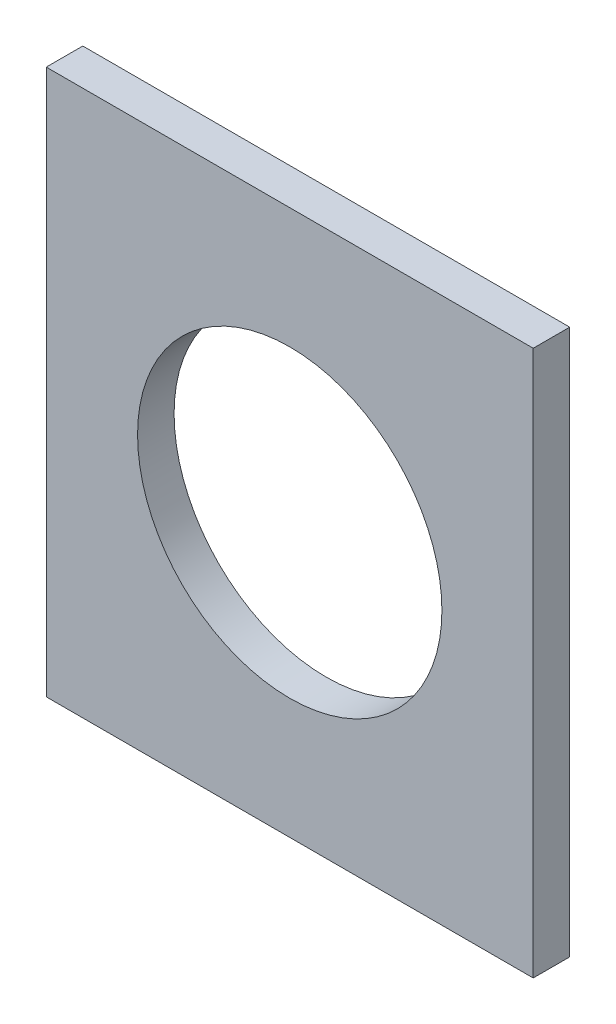
SolidWorks part; units mm, degrees
ref_plane "Plan de face" through (0, 0, 0) normal (0, 0, 1) x (1, 0, 0)
ref_plane "Plan de dessus" through (0, 0, 0) normal (0, 1, 0) x (1, 0, 0)
ref_plane "Plan de droite" through (0, 0, 0) normal (1, 0, 0) x (0, 0, -1)
sketch "Esquisse1" plane through (0, 0, 0) normal (0, 0, 1) x (1, 0, 0)
  line L0 (-30.6386, 15.8612) -> (9.3614, -28.9388) construction
  line L1 (-30.6386, 15.8612) -> (9.3614, 15.8612)
  line L2 (-30.6386, 15.8612) -> (-30.6386, -28.9388)
  line L3 (-30.6386, -28.9388) -> (9.3614, -28.9388)
  line L4 (9.3614, 15.8612) -> (9.3614, -28.9388)
  line L5 (-30.6386, -28.9388) -> (9.3614, 15.8612) construction
  circle A0 centre (-10.6386, -6.5388) radius 12.5
  dimension "D3" = 25
  dimension "D1" = 40
  dimension "D2" = 44.8
extrude "Boss.-Extru.1" add sketch "Esquisse1" along normal blind 3
